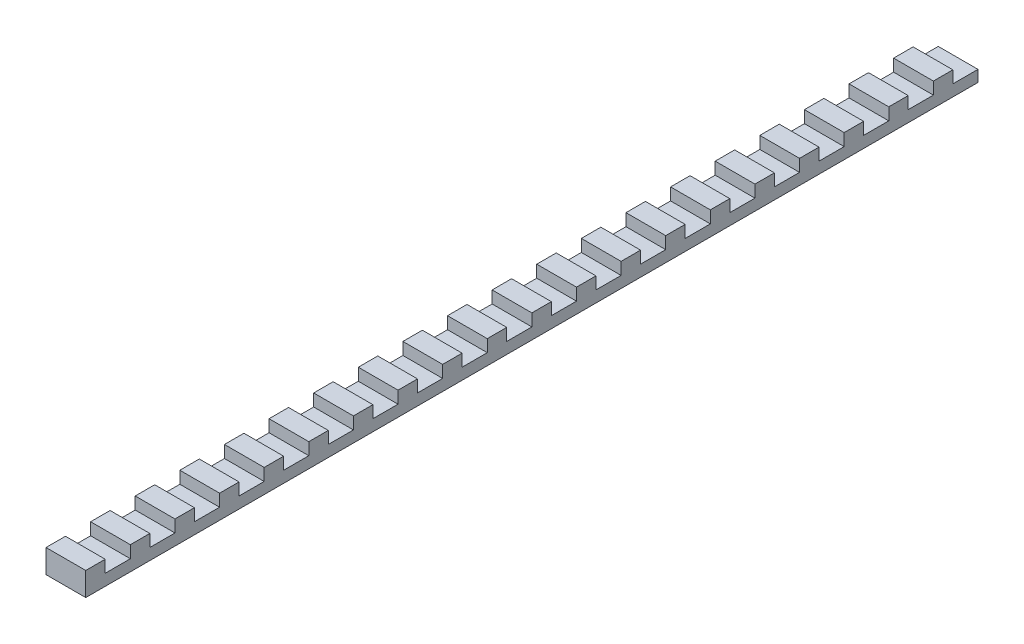
SolidWorks part; units mm, degrees
ref_plane "Front Plane" through (0, 0, 0) normal (0, 0, 1) x (1, 0, 0)
ref_plane "Top Plane" through (0, 0, 0) normal (0, 1, 0) x (1, 0, 0)
ref_plane "Right Plane" through (0, 0, 0) normal (1, 0, 0) x (0, 0, -1)
sketch "Sketch1" plane through (0, 0, 0) normal (1, 0, 0) x (0, 0, -1)
  line L1 (0, 0) -> (4.8, 0)
  line L2 (0, 0) -> (0, 5.8)
  line L3 (0, 5.8) -> (4.8, 5.8)
  line L4 (4.8, 2.8) -> (4.8, 5.8)
  line L5 (0, 0) -> (4.8, 5.8) construction
  line L6 (0, 5.8) -> (4.8, 0) construction
  line L7 (4.8, 0) -> (11, 0)
  line L9 (4.8, 2.8) -> (11, 2.8)
  line L10 (11, 0) -> (11, 2.8)
  line L11 (4.8, 0) -> (11, 2.8) construction
  line L12 (4.8, 2.8) -> (11, 0) construction
  point P4 (2.4, 2.9)
  point P9 (7.9, 1.4)
  dimension "D1" = 5.8
  dimension "D2" = 4.8
  dimension "D3" = 2.8
  dimension "D4" = 11
extrude "Boss-Extrude1" add sketch "Sketch1" along normal blind 9.8
pattern_linear "LPattern1" count 20 spacing 11 along (0, 0, -1) of "Boss-Extrude1"
